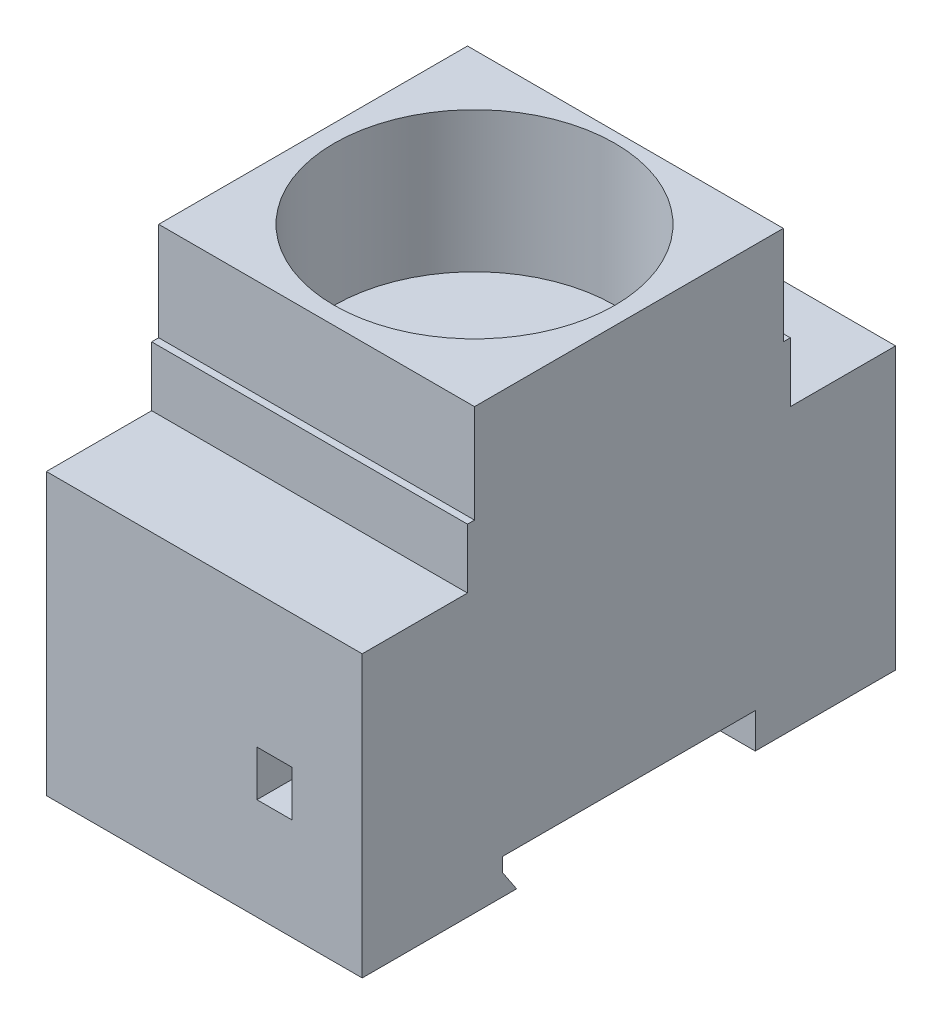
SolidWorks part; units mm, degrees
ref_plane "Спереди" through (0, 0, 0) normal (0, 0, 1) x (1, 0, 0)
ref_plane "Сверху" through (0, 0, 0) normal (0, 1, 0) x (1, 0, 0)
ref_plane "Справа" through (0, 0, 0) normal (1, 0, 0) x (0, 0, -1)
sketch "Эскиз1" plane through (0, 0, 0) normal (1, 0, 0) x (0, 0, -1)
  line L0 (0, 0) -> (0, 40)
  line L1 (0, 40) -> (15, 40)
  line L2 (15, 40) -> (15, 48.5)
  line L3 (15, 48.5) -> (16, 48.5)
  line L4 (16, 48.5) -> (16, 62.5)
  line L5 (16, 62.5) -> (60, 62.5)
  line L6 (60, 62.5) -> (60, 48.5)
  line L7 (60, 48.5) -> (61, 48.5)
  line L8 (61, 48.5) -> (61, 40)
  line L9 (61, 40) -> (76, 40)
  line L10 (76, 40) -> (76, 0)
  line L11 (0, 0) -> (22, 0)
  line L12 (20, 5) -> (20, 3)
  line L13 (20, 5) -> (56, 5)
  line L14 (56, 5) -> (56, 0)
  line L15 (56, 0) -> (76, 0)
  line L16 (20, 3) -> (22, 0)
extrude "Бобышка-Вытянуть1" add sketch "Эскиз1" along normal blind 45
sketch "Эскиз2" plane through (0, 62.5, 0) normal (0, 1, 0) x (1, 0, 0)
  circle A0 centre (22.5, 38.5) radius 20
extrude "Вырез-Вытянуть1" cut sketch "Эскиз2" against normal blind 20
sketch "Эскиз3" plane through (0, 0, 0) normal (0, 0, 1) x (1, 0, 0)
  line L5 (30, 21) -> (35, 21)
  line L6 (30, 21) -> (30, 14.5)
  line L7 (30, 14.5) -> (35, 14.5)
  line L8 (35, 21) -> (35, 14.5)
extrude "Вырез-Вытянуть2" cut sketch "Эскиз3" against normal blind 20
sketch "Эскиз4" plane through (0, 0, -76) normal (0, 0, -1) x (-1, 0, 0)
  line L0 (-35, 21) -> (-30, 21)
  line L1 (-15, 21) -> (-10, 21)
  line L2 (-15, 21) -> (-15, 14.5)
  line L3 (-15, 14.5) -> (-10, 14.5)
  line L4 (-10, 21) -> (-10, 14.5)
  line L5 (-35, 21) -> (-35, 14.5)
  line L6 (-35, 14.5) -> (-30, 14.5)
  line L7 (-30, 21) -> (-30, 14.5)
extrude "Вырез-Вытянуть3" cut sketch "Эскиз4" against normal blind 20
